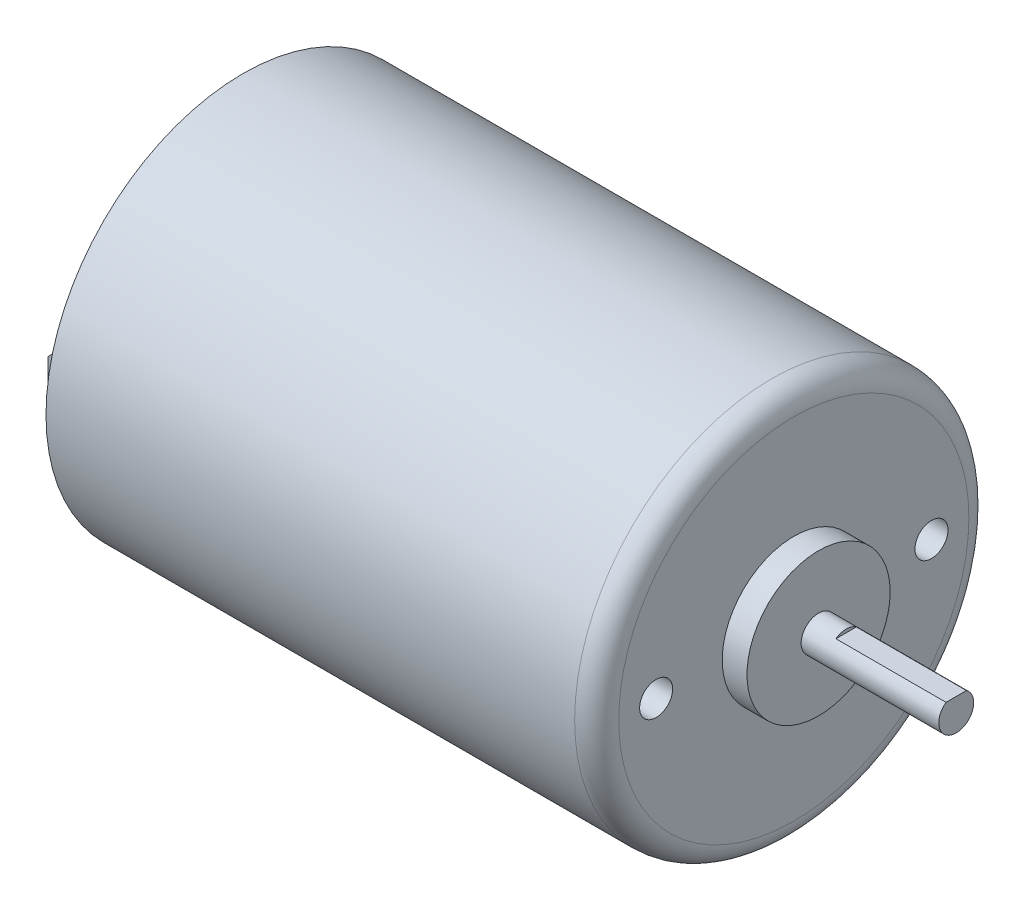
SolidWorks part; units mm, degrees
material "6061 Alloy"
ref_plane "Front Plane" through (0, 0, 0) normal (0, 0, 1) x (1, 0, 0)
ref_plane "Top Plane" through (0, 0, 0) normal (0, 1, 0) x (1, 0, 0)
ref_plane "Right Plane" through (0, 0, 0) normal (1, 0, 0) x (0, 0, -1)
sketch "Sketch1" plane through (0, 0, 0) normal (1, 0, 0) x (0, 0, -1)
  circle A0 centre (0, 0) radius 17.9
  dimension "D1" = 35.8
extrude "Motor-Body" add sketch "Sketch1" along normal mid plane 50
sketch "Sketch2" plane through (-25, 0, 0) normal (-1, 0, 0) x (0, 0, 1)
  circle A0 centre (0, 0) radius 17.2
  circle A1 centre (0, 0) radius 17.9 construction
  dimension "D1" = 0.7
extrude "Cut-Extrude1" cut sketch "Sketch2" against normal blind 0.5
sketch "Sketch3" plane through (-24.5, 0, 0) normal (-1, 0, 0) x (0, 0, 1)
  circle A0 centre (0, 0) radius 12
  dimension "D1" = 24
extrude "Boss-Extrude2" add sketch "Sketch3" along normal mid plane 1
sketch "Sketch4" plane through (-25, 0, 0) normal (-1, 0, 0) x (0, 0, 1)
  circle A0 centre (0, 0) radius 5.1
  dimension "D1" = 10.2
extrude "Boss-Extrude3" add sketch "Sketch4" along normal mid plane 3
fillet "Fillet1" radius 2 1 edges at (25, 0, -17.9)
sketch "Sketch5" plane through (-24.5, 0, 0) normal (-1, 0, 0) x (0, 0, 1)
  line L0 (0, 0) -> (0, 50000) construction
  line L1 (0, 0) -> (50000, 0) construction
  line L2 (14.2, -2) -> (13.7, 2) construction
  line L3 (-14.2, 2) -> (-13.7, 2)
  line L4 (-14.2, 2) -> (-14.2, -2)
  line L5 (-14.2, -2) -> (-13.7, -2)
  line L6 (-13.7, 2) -> (-13.7, -2)
  line L7 (-14.2, 2) -> (-13.7, -2) construction
  line L8 (-14.2, -2) -> (-13.7, 2) construction
  line L9 (14.2, 2) -> (13.7, -2) construction
  line L10 (13.7, 2) -> (13.7, -2)
  line L11 (14.2, -2) -> (13.7, -2)
  line L12 (14.2, 2) -> (14.2, -2)
  line L13 (14.2, 2) -> (13.7, 2)
  circle A1 centre (0, 0) radius 12 construction
  point P6 (-13.95, 0)
  point P17 (13.95, 0)
  dimension "D2" = 13.7
  dimension "D1" = 0.5
  dimension "D3" = 4
extrude "Boss-Extrude4" add sketch "Sketch5" along normal blind 4
chamfer "Chamfer1" distance 1 angle 45 4 edges at (-28.5, 2, 13.95) (-28.5, -2, 13.95) (-28.5, -2, -13.95) (-28.5, 2, -13.95)
sketch "Sketch6" plane through (25, 0, 0) normal (1, 0, 0) x (0, 0, -1)
  line L0 (0, 0) -> (50000, 0) construction
  line L1 (0, 0) -> (0, 50000) construction
  line L2 (-17.9, 0) -> (-17.9, 50000) construction
  circle A0 centre (-12.5, 0) radius 1.5
  circle A1 centre (0, 0) radius 17.9 construction
  circle A2 centre (12.5, 0) radius 1.5
  dimension "D1" = 3
  dimension "D2" = 25
extrude "Mount-Holes" cut sketch "Sketch6" against normal blind 6
sketch "Sketch7" plane through (25, 0, 0) normal (1, 0, 0) x (0, 0, -1)
  circle A0 centre (0, 0) radius 6.5
  dimension "D1" = 13
extrude "Boss-Extrude5" add sketch "Sketch7" along normal mid plane 4.5
sketch "Sketch8" plane through (27.25, 0, 0) normal (1, 0, 0) x (0, 0, -1)
  circle A0 centre (0, 0) radius 1.585
  dimension "D1" = 3.17
extrude "Output-Shaft" add sketch "Sketch8" along normal blind 12.5
sketch "Sketch9" plane through (39.75, 0, 0) normal (1, 0, 0) x (0, 0, -1)
  line L0 (-0.9279, 1.285) -> (0.9279, 1.285)
  line L1 (0, 1.585) -> (-50000, 1.585) construction
  circle A0 centre (0, 0) radius 1.585 construction
  arc A1 (0.9279, 1.285) -> (-0.9279, 1.285) centre (0, 0) ccw
  dimension "D1" = 0.3
extrude "Cut-Extrude3" cut sketch "Sketch9" against normal blind 10
